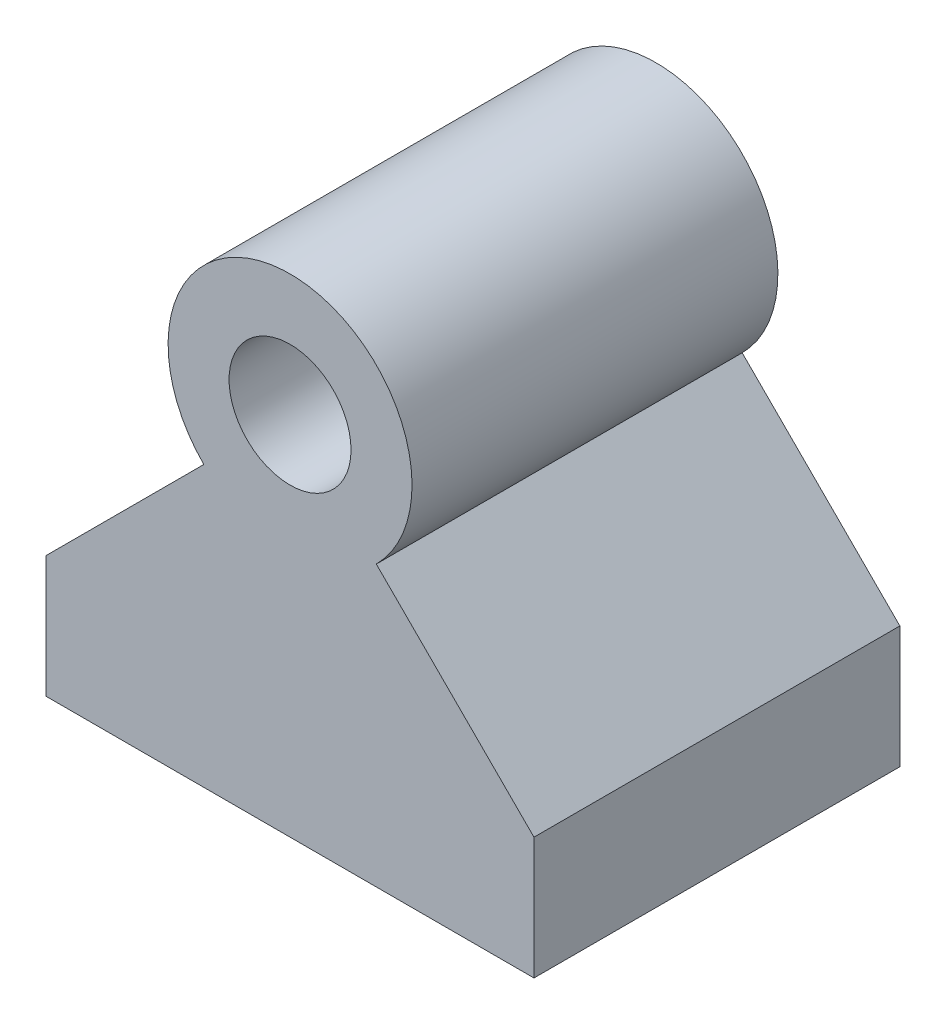
SolidWorks part; units mm, degrees
material "AISI 1020"
ref_plane "Plano frontal" through (0, 0, 0) normal (0, 0, 1) x (1, 0, 0)
ref_plane "Plano superior" through (0, 0, 0) normal (0, 1, 0) x (1, 0, 0)
ref_plane "Plano direito" through (0, 0, 0) normal (1, 0, 0) x (0, 0, -1)
sketch "Esboço1" plane through (0, 0, 0) normal (0, 0, 1) x (1, 0, 0)
  line L0 (-20, 0) -> (20, 0)
  line L1 (20, 0) -> (20, 10)
  line L2 (20, 10) -> (7.0711, 22.9289)
  line L3 (-7.0711, 22.9289) -> (-20, 10)
  line L4 (-20, 10) -> (-20, 0)
  arc A0 (7.0711, 22.9289) -> (-7.0711, 22.9289) centre (0, 30) ccw
  circle A1 centre (0, 30) radius 5
  point P7 (0, 0)
  point P9 (-40.4245, 22.9289)
  dimension "D3" = 10
  dimension "D5" = 10
  dimension "D1" = 90
  dimension "D2" = 40
  dimension "D4" = 30
extrude "Ressalto-extrusão1" add sketch "Esboço1" along normal mid plane 30
